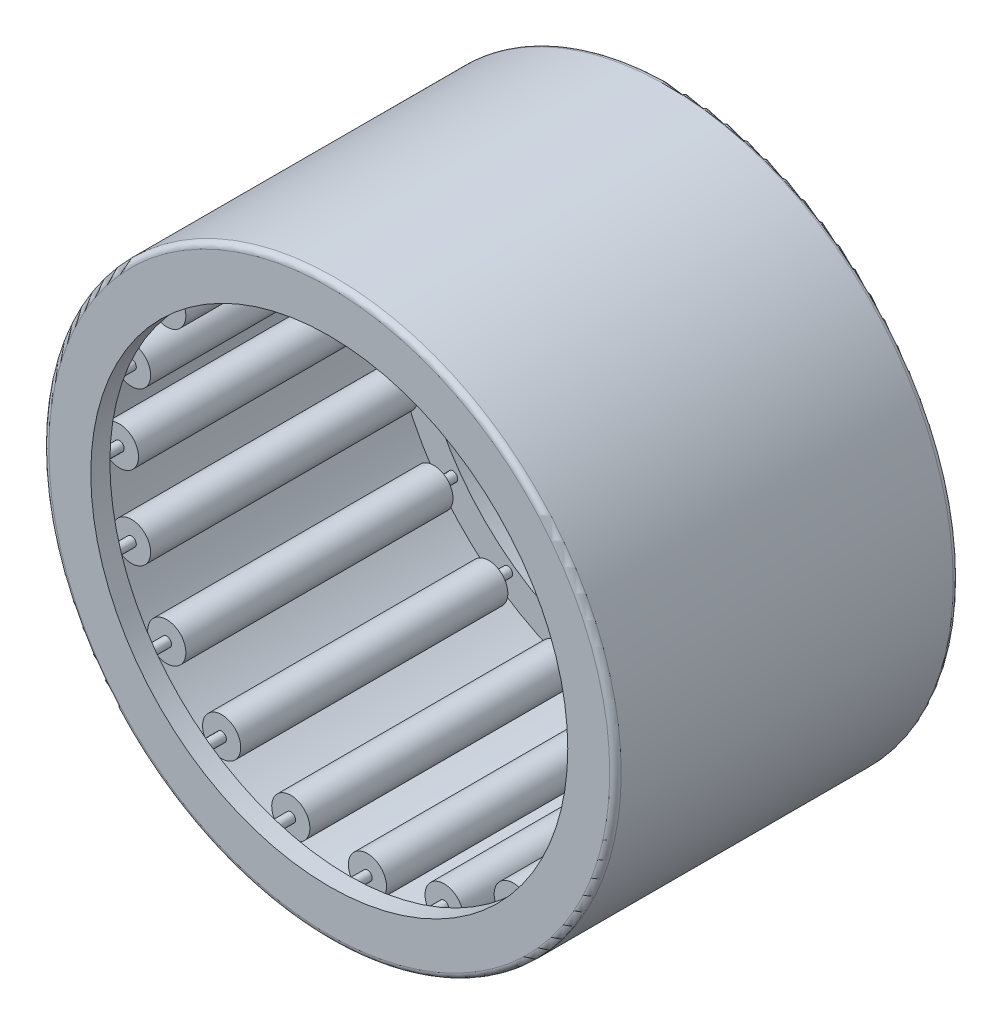
SolidWorks part; units mm, degrees
material "Cast Alloy Steel"
ref_plane "Front Plane" through (0, 0, 0) normal (0, 0, 1) x (1, 0, 0)
ref_plane "Top Plane" through (0, 0, 0) normal (0, 1, 0) x (1, 0, 0)
ref_plane "Right Plane" through (0, 0, 0) normal (1, 0, 0) x (0, 0, -1)
sketch "Sketch1" plane through (0, 0, 0) normal (1, 0, 0) x (0, 0, -1)
  line L0 (-9.525, 0) -> (9.525, 0) construction
  line L1 (0, 0) -> (0, 15.875) construction
  line L2 (-9.525, 0) -> (-9.525, 15.875) construction
  line L3 (-9.525, 15.875) -> (9.525, 15.875)
  line L4 (9.525, 15.875) -> (9.525, 0) construction
  line L5 (9.525, 0) -> (8.4667, 0) construction
  line L6 (8.4667, 0) -> (8.4667, 14.8167) construction
  line L7 (8.4667, 14.8167) -> (-8.4667, 14.8167)
  line L8 (-8.4667, 14.8167) -> (-8.4667, 0) construction
  line L9 (-8.4667, 0) -> (-9.525, 0) construction
  line L10 (-9.525, 15.875) -> (-9.525, 13.2292)
  line L11 (-9.525, 13.2292) -> (-8.4667, 13.2292)
  line L12 (-8.4667, 13.2292) -> (-8.4667, 14.8167)
  line L13 (8.4667, 15.875) -> (8.4667, 14.8167) construction
  line L14 (8.4667, 14.8167) -> (8.4667, 13.2292)
  line L15 (8.4667, 13.2292) -> (9.525, 13.2292)
  line L16 (9.525, 13.2292) -> (9.525, 15.875)
  line L17 (8.4667, 14.8167) -> (8.4667, 13.7583) construction
  line L18 (8.4667, 13.7583) -> (8.4667, 12.7) construction
  line L19 (8.4667, -14.8167) -> (8.4667, -13.7583) construction
  line L20 (8.4667, -15.875) -> (8.4667, -14.8167) construction
  line L21 (9.525, -13.2292) -> (9.525, -15.875) construction
  line L22 (8.4667, -13.2292) -> (9.525, -13.2292) construction
  line L23 (8.4667, -14.8167) -> (8.4667, -13.2292) construction
  line L24 (-8.4667, -13.2292) -> (-8.4667, -14.8167) construction
  line L25 (-9.525, -13.2292) -> (-8.4667, -13.2292) construction
  line L26 (-9.525, -15.875) -> (-9.525, -13.2292) construction
  line L27 (8.4667, -14.8167) -> (-8.4667, -14.8167) construction
  line L28 (-9.525, -15.875) -> (9.525, -15.875) construction
  point P5 (0, 12.7)
  dimension "Width" = 19.05
  dimension "OD" = 31.75
  dimension "Shaft Dia" = 25.4
revolve "Revolve1" add sketch "Sketch1" angle 360 about L0
sketch "Sketch2" plane through (0, 0, 0) normal (1, 0, 0) x (0, 0, -1)
  line L0 (8.4667, 14.8167) -> (-8.4667, 14.8167) construction
  line L1 (-7.4083, 13.7583) -> (7.4083, 13.7583) construction
  line L2 (-7.4083, 13.7583) -> (-7.4083, 14.8167) construction
  line L3 (-7.4083, 14.8167) -> (7.4083, 14.8167)
  line L4 (7.4083, 13.7583) -> (7.4083, 14.8167) construction
  line L5 (8.4667, 13.2292) -> (9.525, 13.2292) construction
  line L6 (-8.4667, 13.7583) -> (-7.4083, 13.7583) construction
  line L7 (7.4083, 13.7583) -> (8.4667, 13.7583) construction
  line L8 (-9.525, 13.2292) -> (-8.4667, 13.2292) construction
  line L9 (-7.4083, 14.0229) -> (-7.4083, 13.4938) construction
  line L10 (-8.4667, 13.7583) -> (-8.4667, 13.2292) construction
  line L11 (-7.4083, 14.8167) -> (-7.4083, 14.0229)
  line L12 (7.4083, 14.8167) -> (7.4083, 14.0229)
  line L13 (7.4083, 14.0229) -> (-7.4083, 14.0229)
  line L14 (0, 14.8167) -> (0, 12.7) construction
  line L15 (-8.4667, 13.2292) -> (-8.4667, 14.8167) construction
  line L16 (-7.4083, 13.4938) -> (-8.4667, 13.4937) construction
  line L17 (0, 0) -> (9.525, 0) construction
  line L18 (-7.4083, -13.4938) -> (-8.4667, -13.4937) construction
  line L19 (0, -14.8167) -> (0, -12.7) construction
  line L20 (-8.4667, -13.7583) -> (-8.4667, -13.2292) construction
  line L21 (-7.4083, -14.0229) -> (-7.4083, -13.4938) construction
  line L22 (7.4083, -13.7583) -> (8.4667, -13.7583) construction
  line L23 (-8.4667, -13.7583) -> (-7.4083, -13.7583) construction
  line L24 (7.4083, -13.7583) -> (7.4083, -14.8167) construction
  line L25 (-7.4083, -13.7583) -> (-7.4083, -14.8167) construction
  line L26 (-7.4083, -13.7583) -> (7.4083, -13.7583) construction
  line L27 (7.4083, -14.0229) -> (-7.4083, -14.0229) construction
  line L28 (7.4083, -14.8167) -> (7.4083, -14.0229) construction
  line L29 (-7.4083, -14.8167) -> (-7.4083, -14.0229) construction
  line L30 (-7.4083, -14.8167) -> (7.4083, -14.8167) construction
  line L31 (9.525, -15.875) -> (9.525, 15.875) construction
  point P16 (0, 13.7583)
revolve "Revolve2" add sketch "Sketch2" angle 360 about L1
sketch "Sketch3" plane through (0, 0, 0) normal (1, 0, 0) x (0, 0, -1)
  line L0 (8.4667, 14.8167) -> (8.4667, 13.2292) construction
  line L1 (-8.4667, 13.7583) -> (8.4667, 13.7583)
  line L2 (-8.4667, 13.7583) -> (-8.4667, 14.0229)
  line L3 (-8.4667, 14.0229) -> (8.4667, 14.0229)
  line L4 (8.4667, 13.7583) -> (8.4667, 14.0229)
  line L5 (0, 0) -> (9.525, 0) construction
  line L6 (9.525, -15.875) -> (9.525, 15.875) construction
  line L7 (8.4667, -13.7583) -> (8.4667, -14.0229) construction
  line L8 (-8.4667, -14.0229) -> (8.4667, -14.0229) construction
  line L9 (-8.4667, -13.7583) -> (-8.4667, -14.0229) construction
  line L10 (-8.4667, -13.7583) -> (8.4667, -13.7583) construction
revolve "Revolve3" add sketch "Sketch3" angle 360 about L1
ref_axis "Axis1" through (0, 0, -9.525) along (0, 0, 1)
pattern_circular "CirPattern1" count 20 every 18 about axis through (0, 0, -9.525) along (0, 0, 1) of bodies 166 167
fillet "Fillet1" radius 0.3175 2 edges at (15.875, 0, -9.525) (15.875, 0, 9.525)
sketch "Sketch4" plane through (0, 0, 0) normal (1, 0, 0) x (0, 0, -1)
  line L1 (9.2075, 12.7) -> (7.4083, 12.7)
  line L2 (9.2075, 12.7) -> (9.2075, 13.2292)
  line L3 (9.2075, 13.2292) -> (7.4083, 13.2292)
  line L4 (7.4083, 12.7) -> (7.4083, 13.2292)
  line L5 (-9.525, 13.2292) -> (-8.4667, 13.2292) construction
  line L6 (9.2075, -15.875) -> (9.2075, 15.875) construction
  line L7 (7.4083, 14.8167) -> (7.4083, 14.0229) construction
revolve "Revolve4" [suppressed] add sketch "Sketch4" angle 360 about L0
sketch "Sketch5" plane through (0, 0, 0) normal (1, 0, 0) x (0, 0, -1)
  line L0 (-9.2075, 15.875) -> (-9.2075, -15.875) construction
  line L1 (-7.4083, 12.7) -> (-9.2075, 12.7)
  line L2 (-7.4083, 12.7) -> (-7.4083, 13.2292)
  line L3 (-7.4083, 13.2292) -> (-9.2075, 13.2292)
  line L4 (-9.2075, 12.7) -> (-9.2075, 13.2292)
  line L6 (-7.4083, 14.8167) -> (-7.4083, 14.0229) construction
  line L7 (-9.525, 13.2292) -> (-8.4667, 13.2292) construction
revolve "Revolve5" [suppressed] add sketch "Sketch5" angle 360 about L0
equation "\"Angle@CirPattern1\" = 360/\"Rollers@CirPattern1\""
equation "\"Rollers@CirPattern1\" = \"OD@Sketch1\"*16"
equation "\"D1@Fillet1\" = \"OD@Sketch1\"*.01"
